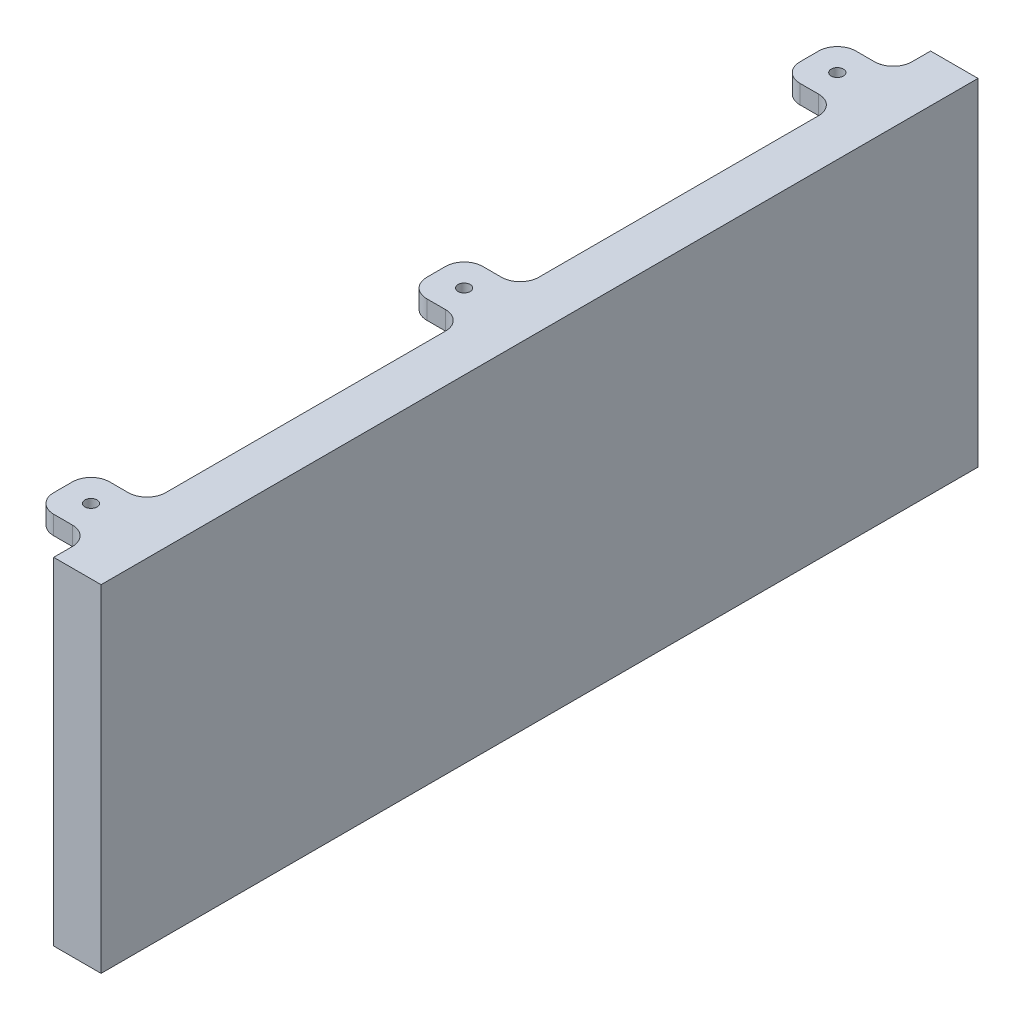
SolidWorks part; units mm, degrees
ref_plane "Front Plane" through (0, 0, 0) normal (0, 0, 1) x (1, 0, 0)
ref_plane "Top Plane" through (0, 0, 0) normal (0, 1, 0) x (1, 0, 0)
ref_plane "Right Plane" through (0, 0, 0) normal (1, 0, 0) x (0, 0, -1)
sketch "Sketch1" plane through (0, 0, 0) normal (0, 1, 0) x (1, 0, 0)
  line L1 (-6.35, -117.475) -> (6.35, -117.475)
  line L2 (-6.35, -117.475) -> (-6.35, 117.475)
  line L3 (-6.35, 117.475) -> (6.35, 117.475)
  line L4 (6.35, -117.475) -> (6.35, 117.475)
  line L5 (-6.35, -117.475) -> (6.35, 117.475) construction
  line L6 (-6.35, 117.475) -> (6.35, -117.475) construction
  point P0 (0, 0)
  dimension "D1" = 234.95
  dimension "D2" = 12.7
extrude "Boss-Extrude1" add sketch "Sketch1" along normal blind 90.2
sketch "Sketch2" plane through (0, 90.2, 0) normal (0, 1, 0) x (1, 0, 0)
  line L0 (-13.65, 0) -> (6.35, 0) construction
  line L1 (6.35, -117.475) -> (6.35, 117.475) construction
  circle A0 centre (-13.65, 0) radius 2.75
  dimension "D1" = 5.5
  dimension "D2" = 20
extrude "Cut-Extrude1" [suppressed] cut sketch "Sketch2" against normal blind 9
sketch "Sketch3" plane through (0, 90.2, 0) normal (0, 1, 0) x (1, 0, 0)
  line L0 (0, 0) -> (-21.35, 0) construction
  line L1 (-6.35, 117.475) -> (-6.35, -117.475) construction
  line L2 (-6.35, 107.475) -> (-21.35, 107.475)
  line L3 (-6.35, 107.475) -> (-6.35, 92.475)
  line L4 (-6.35, 92.475) -> (-21.35, 92.475)
  line L5 (-21.35, 107.475) -> (-21.35, 92.475)
  line L6 (6.35, 117.475) -> (-6.35, 117.475) construction
  line L7 (-21.35, 99.975) -> (6.35, 99.975) construction
  line L8 (6.35, -117.475) -> (6.35, 117.475) construction
  line L9 (-6.35, -92.475) -> (-21.35, -92.475)
  line L10 (-21.35, -107.475) -> (-21.35, -92.475)
  line L11 (-6.35, -107.475) -> (-21.35, -107.475)
  line L12 (-6.35, -107.475) -> (-6.35, -92.475)
  line L14 (-21.35, 7.5) -> (-6.35, 7.5)
  line L15 (-21.35, 7.5) -> (-21.35, -7.5)
  line L16 (-21.35, -7.5) -> (-6.35, -7.5)
  line L17 (-6.35, 7.5) -> (-6.35, -7.5)
  point P23 (-21.35, 0)
  dimension "D1" = 10
  dimension "D2" = 15
  dimension "D3" = 15
extrude "Boss-Extrude2" add sketch "Sketch3" against normal blind 5
hole_wizard "CSK for #4 Flat Head Machine Screw1" positions "Sketch4" profile "Sketch5" countersink size "#4" standard "ANSI Inch" end condition up to next
sketch "Sketch4" plane through (0, 85.2, 0) normal (0, -1, 0) x (1, 0, 0)
  line L0 (-21.35, 99.975) -> (-13.85, 99.975) construction
  line L1 (-21.35, 92.475) -> (-21.35, 107.475) construction
  line L2 (-13.85, 99.975) -> (-13.85, 92.475) construction
  line L3 (-6.35, 92.475) -> (-21.35, 92.475) construction
  line L4 (0, 0) -> (13.705, 0) construction
  line L6 (-13.85, 7.5) -> (-13.85, 0) construction
  line L7 (-21.35, 7.5) -> (-6.35, 7.5) construction
  line L8 (-13.85, 0) -> (-21.35, 0) construction
  line L9 (-21.35, -7.5) -> (-21.35, 7.5) construction
  point P0 (-13.85, 99.975)
  point P16 (-13.85, 0)
  point P26 (-13.85, -99.975)
sketch "Sketch5" plane through (-13.85, 85.2, 99.975) normal (1, 0, 0) x (0, 0, -1)
  line L0 (0, 0) -> (0, 5)
  line L1 (0, 5) -> (1.6319, 5)
  line L2 (1.6319, 5) -> (1.6319, 1.4098)
  line L3 (1.6319, 1.4098) -> (2.8575, 0)
  line L5 (2.8575, 0) -> (0, 0)
  line L6 (-1.632, 1.4098) -> (-2.8575, 0) construction
  line L11 (0, -6.35) -> (0, 107.95) construction
  dimension "Thru Hole Dia." = 3.2639
  dimension "Thru Hole Depth" = 5
  dimension "Near C'Sink Dia." = 5.715
  dimension "Near C'Sink Angle" = 82
fillet "Fillet1" radius 5 12 edges at (-6.35, 87.7, 107.475) (-6.35, 87.7, 92.475) (-6.35, 87.7, -7.5) (-6.35, 87.7, 7.5) (-6.35, 87.7, -92.475) (-6.35, 87.7, -107.475) (-21.35, 87.7, -107.475) (-21.35, 87.7, -92.475) (-21.35, 87.7, -7.5) (-21.35, 87.7, 7.5) (-21.35, 87.7, 92.475) (-21.35, 87.7, 107.475)
fillet "Fillet2" radius 3 3 edges at (-6.35, 85.2, -99.975) (-6.35, 85.2, 0) (-6.35, 85.2, 99.975)
